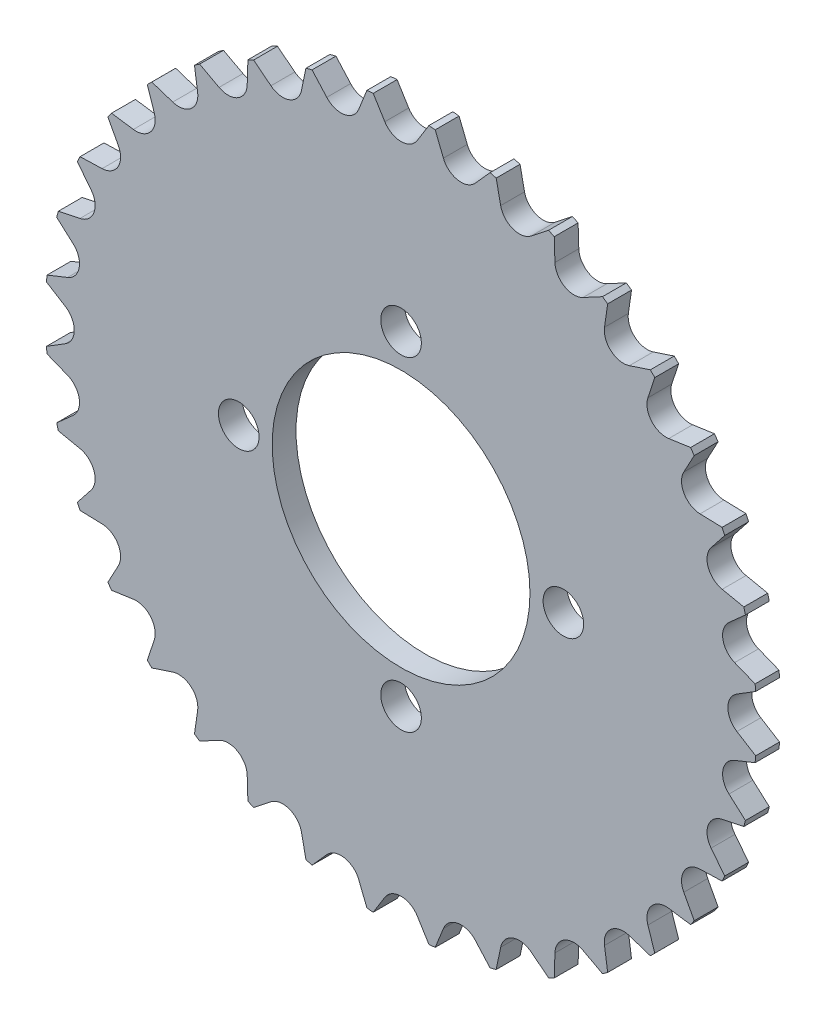
SolidWorks part; units mm, degrees
material "Plain Carbon Steel"
ref_plane "Front Plane" through (0, 0, 0) normal (0, 0, 1) x (1, 0, 0)
ref_plane "Top Plane" through (0, 0, 0) normal (0, 1, 0) x (1, 0, 0)
ref_plane "Right Plane" through (0, 0, 0) normal (1, 0, 0) x (0, 0, -1)
sketch "Sketch1" plane through (0, 0, 0) normal (0, 0, 1) x (1, 0, 0)
  line L0 (3.4006, 70.3439) -> (6.0855, 74.679)
  line L1 (3.4006, 70.3439) -> (8.8661, 69.8657) construction
  line L2 (6.9749, 74.6012) -> (8.8661, 69.8657)
  line L3 (3.4006, 70.3439) -> (0, 0) construction
  line L4 (0, 0) -> (8.8661, 69.8657) construction
  line L5 (15.5641, 68.6847) -> (18.9609, 72.4877)
  line L6 (19.8233, 72.2567) -> (20.8635, 67.2647)
  line L7 (27.2546, 64.9386) -> (31.2602, 68.094)
  line L8 (32.0693, 67.7166) -> (32.2269, 62.6199)
  line L9 (38.117, 59.2193) -> (42.6097, 61.6312)
  line L10 (43.341, 61.1191) -> (42.6111, 56.0725)
  line L11 (47.8212, 51.7007) -> (52.6645, 53.2958)
  line L12 (53.2958, 52.6645) -> (51.7007, 47.8212)
  line L13 (56.0725, 42.6111) -> (61.1191, 43.341)
  line L14 (61.6312, 42.6097) -> (59.2193, 38.117)
  line L15 (62.6199, 32.2269) -> (67.7166, 32.0693)
  line L16 (68.094, 31.2602) -> (64.9386, 27.2546)
  line L17 (67.2647, 20.8635) -> (72.2567, 19.8233)
  line L18 (72.4877, 18.9609) -> (68.6847, 15.5641)
  line L19 (69.8657, 8.8661) -> (74.6012, 6.9749)
  line L20 (74.679, 6.0855) -> (70.3439, 3.4006)
  line L21 (70.3439, -3.4006) -> (74.679, -6.0855)
  line L22 (74.6012, -6.9749) -> (69.8657, -8.8661)
  line L23 (68.6847, -15.5641) -> (72.4877, -18.9609)
  line L24 (72.2567, -19.8233) -> (67.2647, -20.8635)
  line L25 (64.9386, -27.2546) -> (68.094, -31.2602)
  line L26 (67.7166, -32.0693) -> (62.6199, -32.2269)
  line L27 (59.2193, -38.117) -> (61.6312, -42.6097)
  line L28 (61.1191, -43.341) -> (56.0725, -42.6111)
  line L29 (51.7007, -47.8212) -> (53.2958, -52.6645)
  line L30 (52.6645, -53.2958) -> (47.8212, -51.7007)
  line L31 (42.6111, -56.0725) -> (43.341, -61.1191)
  line L32 (42.6097, -61.6312) -> (38.117, -59.2193)
  line L33 (32.2269, -62.6199) -> (32.0693, -67.7166)
  line L34 (31.2602, -68.094) -> (27.2546, -64.9386)
  line L35 (20.8635, -67.2647) -> (19.8233, -72.2567)
  line L36 (18.9609, -72.4877) -> (15.5641, -68.6847)
  line L37 (8.8661, -69.8657) -> (6.9749, -74.6012)
  line L38 (6.0855, -74.679) -> (3.4006, -70.3439)
  line L39 (-3.4006, -70.3439) -> (-6.0855, -74.679)
  line L40 (-6.9749, -74.6012) -> (-8.8661, -69.8657)
  line L41 (-15.5641, -68.6847) -> (-18.9609, -72.4877)
  line L42 (-19.8233, -72.2567) -> (-20.8635, -67.2647)
  line L43 (-27.2546, -64.9386) -> (-31.2602, -68.094)
  line L44 (-32.0693, -67.7166) -> (-32.2269, -62.6199)
  line L45 (-38.117, -59.2193) -> (-42.6097, -61.6312)
  line L46 (-43.341, -61.1191) -> (-42.6111, -56.0725)
  line L47 (-47.8212, -51.7007) -> (-52.6645, -53.2958)
  line L48 (-53.2958, -52.6645) -> (-51.7007, -47.8212)
  line L49 (-56.0725, -42.6111) -> (-61.1191, -43.341)
  line L50 (-61.6312, -42.6097) -> (-59.2193, -38.117)
  line L51 (-62.6199, -32.2269) -> (-67.7166, -32.0693)
  line L52 (-68.094, -31.2602) -> (-64.9386, -27.2546)
  line L53 (-67.2647, -20.8635) -> (-72.2567, -19.8233)
  line L54 (-72.4877, -18.9609) -> (-68.6847, -15.5641)
  line L55 (-69.8657, -8.8661) -> (-74.6012, -6.9749)
  line L56 (-74.679, -6.0855) -> (-70.3439, -3.4006)
  line L57 (-70.3439, 3.4006) -> (-74.679, 6.0855)
  line L58 (-74.6012, 6.9749) -> (-69.8657, 8.8661)
  line L59 (-68.6847, 15.5641) -> (-72.4877, 18.9609)
  line L60 (-72.2567, 19.8233) -> (-67.2647, 20.8635)
  line L61 (-64.9386, 27.2546) -> (-68.094, 31.2602)
  line L62 (-67.7166, 32.0693) -> (-62.6199, 32.2269)
  line L63 (-59.2193, 38.117) -> (-61.6312, 42.6097)
  line L64 (-61.1191, 43.341) -> (-56.0725, 42.6111)
  line L65 (-51.7007, 47.8212) -> (-53.2958, 52.6645)
  line L66 (-52.6645, 53.2958) -> (-47.8212, 51.7007)
  line L67 (-42.6111, 56.0725) -> (-43.341, 61.1191)
  line L68 (-42.6097, 61.6312) -> (-38.117, 59.2193)
  line L69 (-32.2269, 62.6199) -> (-32.0693, 67.7166)
  line L70 (-31.2602, 68.094) -> (-27.2546, 64.9386)
  line L71 (-20.8635, 67.2647) -> (-19.8233, 72.2567)
  line L72 (-18.9609, 72.4877) -> (-15.5641, 68.6847)
  line L73 (-8.8661, 69.8657) -> (-6.9749, 74.6012)
  line L74 (-6.0855, 74.679) -> (-3.4006, 70.3439)
  line L83 (0, 72.45) -> (0, 0) construction
  line L84 (0, 0) -> (6.5105, 74.4157) construction
  circle A0 centre (0, 0) radius 72.45 construction
  arc A1 (-3.9985, 72.3396) -> (3.4006, 70.3439) centre (0, 72.45) ccw
  arc A2 (4.6139, 72.3029) -> (8.0115, 72.0057) centre (0, 0) cw
  arc A3 (6.0855, 74.679) -> (6.9749, 74.6012) centre (6.5105, 74.4157) cw
  arc A4 (8.6239, 71.9349) -> (15.5641, 68.6847) centre (12.5808, 71.3493) ccw
  arc A5 (18.9609, 72.4877) -> (19.8233, 72.2567) centre (19.3338, 72.1547) cw
  arc A6 (20.9843, 69.3445) -> (27.2546, 64.9386) centre (24.7794, 68.0807) ccw
  arc A7 (31.2602, 68.094) -> (32.0693, 67.7166) centre (31.5696, 67.7012) cw
  arc A8 (32.707, 64.6472) -> (38.117, 59.2193) centre (36.225, 62.7435) ccw
  arc A9 (42.6097, 61.6312) -> (43.341, 61.1191) centre (42.8462, 61.1907) cw
  arc A10 (43.436, 57.9855) -> (47.8212, 51.7007) centre (46.57, 55.4999) ccw
  arc A11 (52.6645, 53.2958) -> (53.2958, 52.6645) centre (52.8209, 52.8209) cw
  arc A12 (52.8452, 49.562) -> (56.0725, 42.6111) centre (55.4999, 46.57) ccw
  arc A13 (61.1191, 43.341) -> (61.6312, 42.6097) centre (61.1907, 42.8462) cw
  arc A14 (60.6487, 39.6326) -> (62.6199, 32.2269) centre (62.7435, 36.225) ccw
  arc A15 (67.7166, 32.0693) -> (68.094, 31.2602) centre (67.7012, 31.5696) cw
  arc A16 (66.6094, 28.4989) -> (67.2647, 20.8635) centre (68.0807, 24.7794) ccw
  arc A17 (72.2567, 19.8233) -> (72.4877, 18.9609) centre (72.1547, 19.3338) cw
  arc A18 (70.5463, 16.4994) -> (69.8657, 8.8661) centre (71.3493, 12.5808) ccw
  arc A19 (74.6012, 6.9749) -> (74.679, 6.0855) centre (74.4157, 6.5105) cw
  arc A20 (72.3396, 3.9985) -> (70.3439, -3.4006) centre (72.45, 0) ccw
  arc A21 (74.679, -6.0855) -> (74.6012, -6.9749) centre (74.4157, -6.5105) cw
  arc A22 (71.9349, -8.6239) -> (68.6847, -15.5641) centre (71.3493, -12.5808) ccw
  arc A23 (72.4877, -18.9609) -> (72.2567, -19.8233) centre (72.1547, -19.3338) cw
  arc A24 (69.3445, -20.9843) -> (64.9386, -27.2546) centre (68.0807, -24.7794) ccw
  arc A25 (68.094, -31.2602) -> (67.7166, -32.0693) centre (67.7012, -31.5696) cw
  arc A26 (64.6472, -32.707) -> (59.2193, -38.117) centre (62.7435, -36.225) ccw
  arc A27 (61.6312, -42.6097) -> (61.1191, -43.341) centre (61.1907, -42.8462) cw
  arc A28 (57.9855, -43.436) -> (51.7007, -47.8212) centre (55.4999, -46.57) ccw
  arc A29 (53.2958, -52.6645) -> (52.6645, -53.2958) centre (52.8209, -52.8209) cw
  arc A30 (49.562, -52.8452) -> (42.6111, -56.0725) centre (46.57, -55.4999) ccw
  arc A31 (43.341, -61.1191) -> (42.6097, -61.6312) centre (42.8462, -61.1907) cw
  arc A32 (39.6326, -60.6487) -> (32.2269, -62.6199) centre (36.225, -62.7435) ccw
  arc A33 (32.0693, -67.7166) -> (31.2602, -68.094) centre (31.5696, -67.7012) cw
  arc A34 (28.4989, -66.6094) -> (20.8635, -67.2647) centre (24.7794, -68.0807) ccw
  arc A35 (19.8233, -72.2567) -> (18.9609, -72.4877) centre (19.3338, -72.1547) cw
  arc A36 (16.4994, -70.5463) -> (8.8661, -69.8657) centre (12.5808, -71.3493) ccw
  arc A37 (6.9749, -74.6012) -> (6.0855, -74.679) centre (6.5105, -74.4157) cw
  arc A38 (3.9985, -72.3396) -> (-3.4006, -70.3439) centre (0, -72.45) ccw
  arc A39 (-6.0855, -74.679) -> (-6.9749, -74.6012) centre (-6.5105, -74.4157) cw
  arc A40 (-8.6239, -71.9349) -> (-15.5641, -68.6847) centre (-12.5808, -71.3493) ccw
  arc A41 (-18.9609, -72.4877) -> (-19.8233, -72.2567) centre (-19.3338, -72.1547) cw
  arc A42 (-20.9843, -69.3445) -> (-27.2546, -64.9386) centre (-24.7794, -68.0807) ccw
  arc A43 (-31.2602, -68.094) -> (-32.0693, -67.7166) centre (-31.5696, -67.7012) cw
  arc A44 (-32.707, -64.6472) -> (-38.117, -59.2193) centre (-36.225, -62.7435) ccw
  arc A45 (-42.6097, -61.6312) -> (-43.341, -61.1191) centre (-42.8462, -61.1907) cw
  arc A46 (-43.436, -57.9855) -> (-47.8212, -51.7007) centre (-46.57, -55.4999) ccw
  arc A47 (-52.6645, -53.2958) -> (-53.2958, -52.6645) centre (-52.8209, -52.8209) cw
  arc A48 (-52.8452, -49.562) -> (-56.0725, -42.6111) centre (-55.4999, -46.57) ccw
  arc A49 (-61.1191, -43.341) -> (-61.6312, -42.6097) centre (-61.1907, -42.8462) cw
  arc A50 (-60.6487, -39.6326) -> (-62.6199, -32.2269) centre (-62.7435, -36.225) ccw
  arc A51 (-67.7166, -32.0693) -> (-68.094, -31.2602) centre (-67.7012, -31.5696) cw
  arc A52 (-66.6094, -28.4989) -> (-67.2647, -20.8635) centre (-68.0807, -24.7794) ccw
  arc A53 (-72.2567, -19.8233) -> (-72.4877, -18.9609) centre (-72.1547, -19.3338) cw
  arc A54 (-70.5463, -16.4994) -> (-69.8657, -8.8661) centre (-71.3493, -12.5808) ccw
  arc A55 (-74.6012, -6.9749) -> (-74.679, -6.0855) centre (-74.4157, -6.5105) cw
  arc A56 (-72.3396, -3.9985) -> (-70.3439, 3.4006) centre (-72.45, 0) ccw
  arc A57 (-74.679, 6.0855) -> (-74.6012, 6.9749) centre (-74.4157, 6.5105) cw
  arc A58 (-71.9349, 8.6239) -> (-68.6847, 15.5641) centre (-71.3493, 12.5808) ccw
  arc A59 (-72.4877, 18.9609) -> (-72.2567, 19.8233) centre (-72.1547, 19.3338) cw
  arc A60 (-69.3445, 20.9843) -> (-64.9386, 27.2546) centre (-68.0807, 24.7794) ccw
  arc A61 (-68.094, 31.2602) -> (-67.7166, 32.0693) centre (-67.7012, 31.5696) cw
  arc A62 (-64.6472, 32.707) -> (-59.2193, 38.117) centre (-62.7435, 36.225) ccw
  arc A63 (-61.6312, 42.6097) -> (-61.1191, 43.341) centre (-61.1907, 42.8462) cw
  arc A64 (-57.9855, 43.436) -> (-51.7007, 47.8212) centre (-55.4999, 46.57) ccw
  arc A65 (-53.2958, 52.6645) -> (-52.6645, 53.2958) centre (-52.8209, 52.8209) cw
  arc A66 (-49.562, 52.8452) -> (-42.6111, 56.0725) centre (-46.57, 55.4999) ccw
  arc A67 (-43.341, 61.1191) -> (-42.6097, 61.6312) centre (-42.8462, 61.1907) cw
  arc A68 (-39.6326, 60.6487) -> (-32.2269, 62.6199) centre (-36.225, 62.7435) ccw
  arc A69 (-32.0693, 67.7166) -> (-31.2602, 68.094) centre (-31.5696, 67.7012) cw
  arc A70 (-28.4989, 66.6094) -> (-20.8635, 67.2647) centre (-24.7794, 68.0807) ccw
  arc A71 (-19.8233, 72.2567) -> (-18.9609, 72.4877) centre (-19.3338, 72.1547) cw
  arc A72 (-16.4994, 70.5463) -> (-8.8661, 69.8657) centre (-12.5808, 71.3493) ccw
  arc A73 (-6.9749, 74.6012) -> (-6.0855, 74.679) centre (-6.5105, 74.4157) cw
  point P289 (0, 0)
  dimension "D1" = 144.9
  dimension "D2" = 4
  dimension "D5" = 0.5
  dimension "D6" = 74.7
  dimension "D3" = 5
  dimension "D4" = 36
extrude "Boss-Extrude1" add sketch "Sketch1" along normal blind 5
sketch "Sketch5" plane through (0, 0, 0) normal (0, 0, -1) x (-1, 0, 0)
  line L0 (0, 68.45) -> (2.9886, 68.1885)
  line L1 (0, 68.45) -> (0.611, 75.4338)
  line L2 (11.8862, 67.4101) -> (12.4972, 74.3939)
  line L3 (0.611, 75.4338) -> (12.4972, 74.3939)
  line L4 (8.8976, 67.6716) -> (11.8862, 67.4101)
  arc A0 (2.9886, 68.1885) -> (8.8976, 67.6716) centre (6.3977, 73.1259) ccw
  arc A3 (-3.4006, 70.3439) -> (3.4006, 70.3439) centre (0, 72.45) ccw construction
  arc A5 (-3.4006, 70.3439) -> (3.4006, 70.3439) centre (0, 72.45) ccw construction
  arc A7 (8.8661, 69.8657) -> (15.5641, 68.6847) centre (12.5808, 71.3493) ccw construction
  arc A8 (6.9749, 74.6012) -> (6.0855, 74.679) centre (6.5105, 74.4157) ccw construction
  point P19 (0, 68.45)
  point P22 (11.8862, 67.4101)
  dimension "D2" = 3
  dimension "D3" = 3
  dimension "D4" = 6
extrude "Cut-Extrude2" [suppressed] cut sketch "Sketch5" against normal blind 10
sketch "Sketch9" plane through (0, 0, 0) normal (0, 0, -1) x (-1, 0, 0)
  circle A0 centre (0, 0) radius 74.5
  circle A1 centre (0, 0) radius 100
  dimension "D1" = 149
  dimension "D2" = 200
extrude "Cut-Extrude5" cut sketch "Sketch9" against normal blind 10
sketch "Sketch10" plane through (0, 0, 5) normal (0, 0, 1) x (1, 0, 0)
  circle A0 centre (0, 0) radius 27
  circle A1 centre (0, 34) radius 4.25
  circle A2 centre (34, 0) radius 4.25
  circle A3 centre (0, -34) radius 4.25
  circle A4 centre (-34, 0) radius 4.25
  point P14 (0, 0)
  dimension "D1" = 54
  dimension "D2" = 8.5
  dimension "D3" = 34
  dimension "D4" = 4
extrude "Cut-Extrude6" cut sketch "Sketch10" against normal through all
sketch "Sketch11" plane through (0, 0, 5) normal (0, 0, 1) x (1, 0, 0)
  line L1 (88.2775, 0) -> (-102.8822, 0)
  line L2 (88.2775, 0) -> (88.2775, -76.2691)
  line L3 (88.2775, -76.2691) -> (-102.8822, -76.2691)
  line L4 (-102.8822, 0) -> (-102.8822, -76.2691)
  circle A0 centre (0, 0) radius 55
  dimension "D1" = 110
extrude "Cut-Extrude7" [suppressed] cut sketch "Sketch11" against normal blind 10 contours L1 A0 | A0 L1 L4 L3 L2 | L1 A0
equation "\"Teeth\"= 36"
equation "\"D4@Sketch1\"=\"Teeth\""
equation "\"D6@Sketch1\"=83/40*\"Teeth\""
equation "\"D1@Sketch1\"=161/40*\"Teeth\""
equation "\"D3@Sketch1\"=4.5/\"Teeth\"*40"
